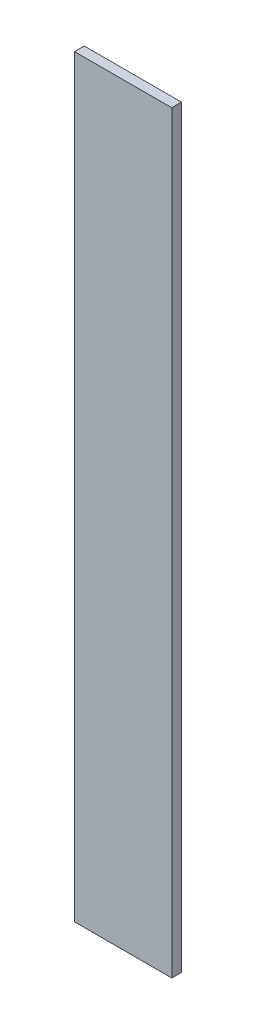
SolidWorks part; units mm, degrees
ref_plane "Plano frontal" through (0, 0, 0) normal (0, 0, 1) x (1, 0, 0)
ref_plane "Plano superior" through (0, 0, 0) normal (0, 1, 0) x (1, 0, 0)
ref_plane "Plano direito" through (0, 0, 0) normal (1, 0, 0) x (0, 0, -1)
sketch "Esboço1" plane through (0, 0, 0) normal (0, 1, 0) x (1, 0, 0)
  line L1 (-129.6089, 67.4581) -> (70.3911, 67.4581)
  line L2 (-129.6089, 67.4581) -> (-129.6089, 47.4581)
  line L3 (-129.6089, 47.4581) -> (70.3911, 47.4581)
  line L4 (70.3911, 67.4581) -> (70.3911, 47.4581)
  dimension "D1" = 200
  dimension "D2" = 20
extrude "Ressalto-extrusão1" add sketch "Esboço1" along normal blind 1550
